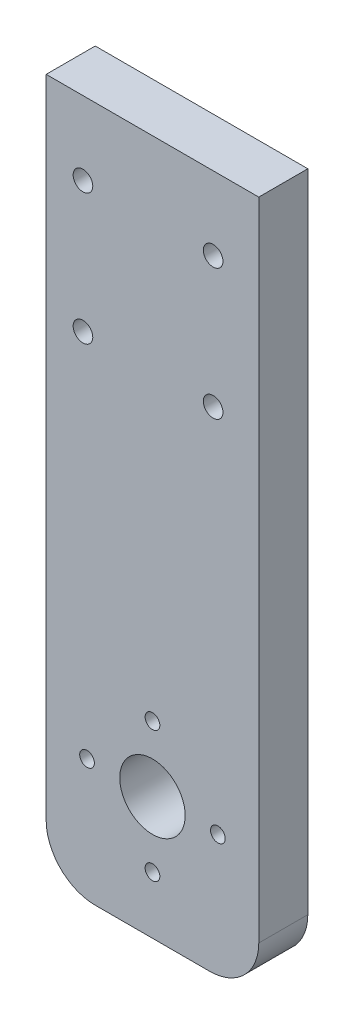
SolidWorks part; units mm, degrees
ref_plane "Plan de face" through (0, 0, 0) normal (0, 0, 1) x (1, 0, 0)
ref_plane "Plan de dessus" through (0, 0, 0) normal (0, 1, 0) x (1, 0, 0)
ref_plane "Plan de droite" through (0, 0, 0) normal (1, 0, 0) x (0, 0, -1)
sketch "Esquisse1" plane through (0, 0, 0) normal (0, 0, 1) x (1, 0, 0)
  line L0 (24.9164, -77.5735) -> (24.9164, 1.4265)
  line L1 (50.9164, 1.4265) -> (24.9164, 1.4265)
  line L2 (37.9164, 189.4329) -> (37.9164, -108.4772) construction
  line L3 (30.9164, -83.5735) -> (44.9164, -83.5735)
  line L11 (50.9164, -77.5735) -> (50.9164, 1.4265)
  arc A0 (44.9164, -83.5735) -> (50.9164, -77.5735) centre (44.9164, -77.5735) ccw
  arc A1 (24.9164, -77.5735) -> (30.9164, -83.5735) centre (30.9164, -77.5735) ccw
  circle A2 centre (29.9164, -68.5735) radius 0.9
  circle A3 centre (37.9164, -60.5735) radius 0.9
  circle A4 centre (45.9164, -68.5735) radius 0.9
  circle A5 centre (37.9164, -76.5735) radius 0.9
  circle A7 centre (37.9164, -68.5735) radius 4
  point P6 (50.9164, -83.5735)
  dimension "D3" = 6
  dimension "D6" = 1.8
  dimension "D7" = 1.8
  dimension "D8" = 1.8
  dimension "D9" = 1.8
  dimension "D4" = 8
  dimension "D1" = 85
  dimension "D5" = 15
extrude "Boss.-Extru.1" add sketch "Esquisse1" along normal blind 6
sketch "Esquisse2" plane through (0, 0, 0) normal (0, 0, -1) x (-1, 0, 0)
  line L2 (-24.9164, 1.4265) -> (-24.9164, -77.5735) construction
  line L3 (-50.9164, 1.4265) -> (-24.9164, 1.4265) construction
  line L5 (-50.9164, -77.5735) -> (-50.9164, 1.4265) construction
  circle A0 centre (-45.3364, -7.5735) radius 1.2
  circle A1 centre (-29.4164, -7.5735) radius 1.2
  circle A2 centre (-45.3364, -23.5735) radius 1.2
  circle A3 centre (-29.4164, -23.5735) radius 1.2
  dimension "D1" = 2.4
  dimension "D2" = 2.4
  dimension "D3" = 2.4
  dimension "D4" = 2.4
  dimension "D5" = 4.5
  dimension "D6" = 4.5
  dimension "D7" = 9
  dimension "D8" = 9
  dimension "D9" = 16
  dimension "D10" = 16
  dimension "D11" = 5.58
  dimension "D12" = 5.58
extrude "Enlèv. mat.-Extru.1" cut sketch "Esquisse2" against normal blind 10
